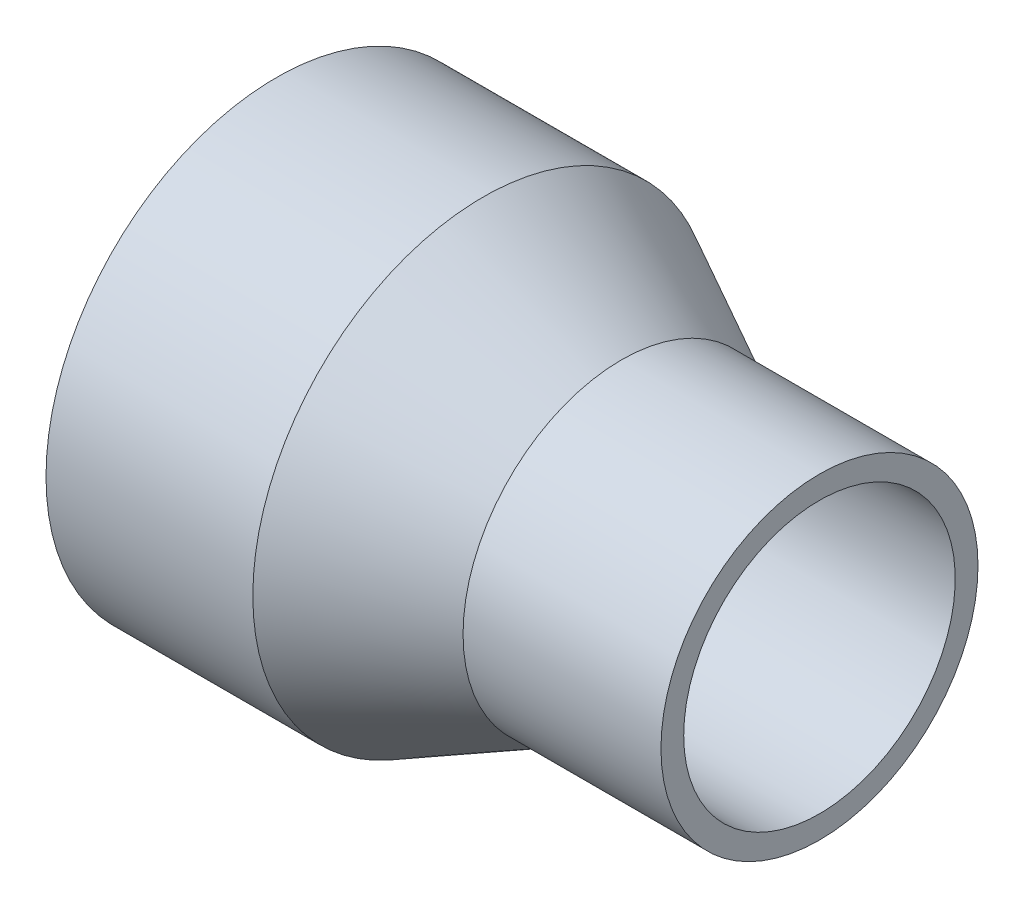
SolidWorks part; units mm, degrees
ref_plane "Front Plane" through (0, 0, 0) normal (0, 0, 1) x (1, 0, 0)
ref_plane "Top Plane" through (0, 0, 0) normal (0, 1, 0) x (1, 0, 0)
ref_plane "Right Plane" through (0, 0, 0) normal (1, 0, 0) x (0, 0, -1)
sketch "Sketch1" plane through (0, 0, 0) normal (0, 0, 1) x (1, 0, 0)
  line L1 (0, 0) -> (101.6, 0) construction
  line L2 (0, 38.1) -> (4.4316, 38.1)
  line L3 (0, 38.1) -> (0, 43.1)
  line L4 (0, 43.1) -> (4.4316, 43.1)
  line L5 (101.6, 0) -> (101.6, 25.4) construction
  line L6 (50.8, 36.8111) -> (50.8, 0) construction
  line L7 (101.6, 25.4) -> (64.5764, 25.4)
  line L8 (64.5764, 25.4) -> (38.6914, 38.1)
  line L9 (38.6914, 38.1) -> (0, 38.1)
  line L10 (4.4316, 43.1) -> (38.6914, 43.1)
  line L11 (38.6914, 43.1) -> (64.5764, 29.656)
  line L12 (64.5764, 29.656) -> (101.6, 29.656)
  line L13 (101.6, 29.656) -> (101.6, 25.4)
revolve "Revolve1" add sketch "Sketch1" angle 360 about L1
